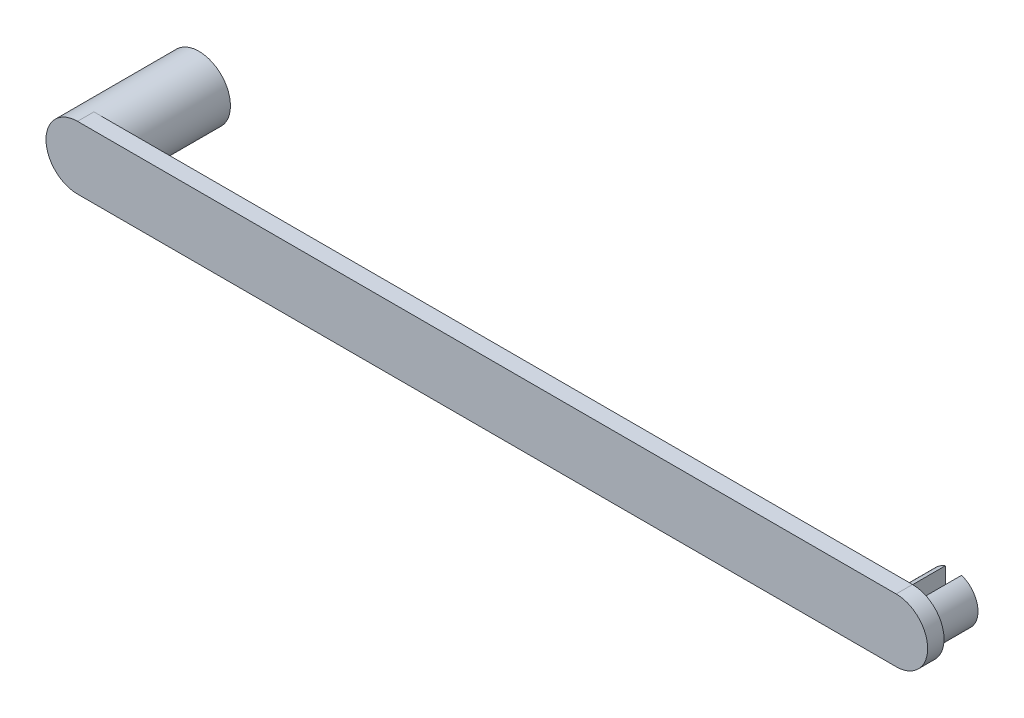
SolidWorks part; units mm, degrees
ref_plane "Front Plane" through (0, 0, 0) normal (0, 0, 1) x (1, 0, 0)
ref_plane "Top Plane" through (0, 0, 0) normal (0, 1, 0) x (1, 0, 0)
ref_plane "Right Plane" through (0, 0, 0) normal (1, 0, 0) x (0, 0, -1)
sketch "Sketch1" plane through (0, 0, 0) normal (0, 0, 1) x (1, 0, 0)
  circle A0 centre (0, 0) radius 3.85
extrude "Boss-Extrude1" add sketch "Sketch1" along normal blind 12.83
sketch "Sketch2" plane through (0, 0, 12.83) normal (0, 0, 1) x (1, 0, 0)
  line L2 (0, 3.85) -> (100, 3.85)
  line L3 (0, 3.85) -> (0, -3.85)
  line L4 (0, -3.85) -> (100, -3.85)
  circle A1 centre (100, 0) radius 3.85
  circle A2 centre (0, 0) radius 3.85 construction
  circle M3 centre (0, 0) radius 3.85
extrude "Boss-Extrude3" add sketch "Sketch2" along normal blind 2 contours A1 | A1 L2 L4 M3 | L3 M3 | L3 M3
sketch "Sketch3" plane through (0, 0, 12.83) normal (0, 0, -1) x (-1, 0, 0)
  line L1 (-99, 3) -> (-101, 3)
  line L2 (-99, 3) -> (-99, -3)
  line L3 (-99, -3) -> (-101, -3)
  line L4 (-101, 3) -> (-101, -3)
  line L5 (-99, 3) -> (-101, -3) construction
  line L6 (-99, -3) -> (-101, 3) construction
  circle A1 centre (-100, 0) radius 3
extrude "Boss-Extrude5" add sketch "Sketch3" along normal blind 5 contours L4 A1 | L2 A1
